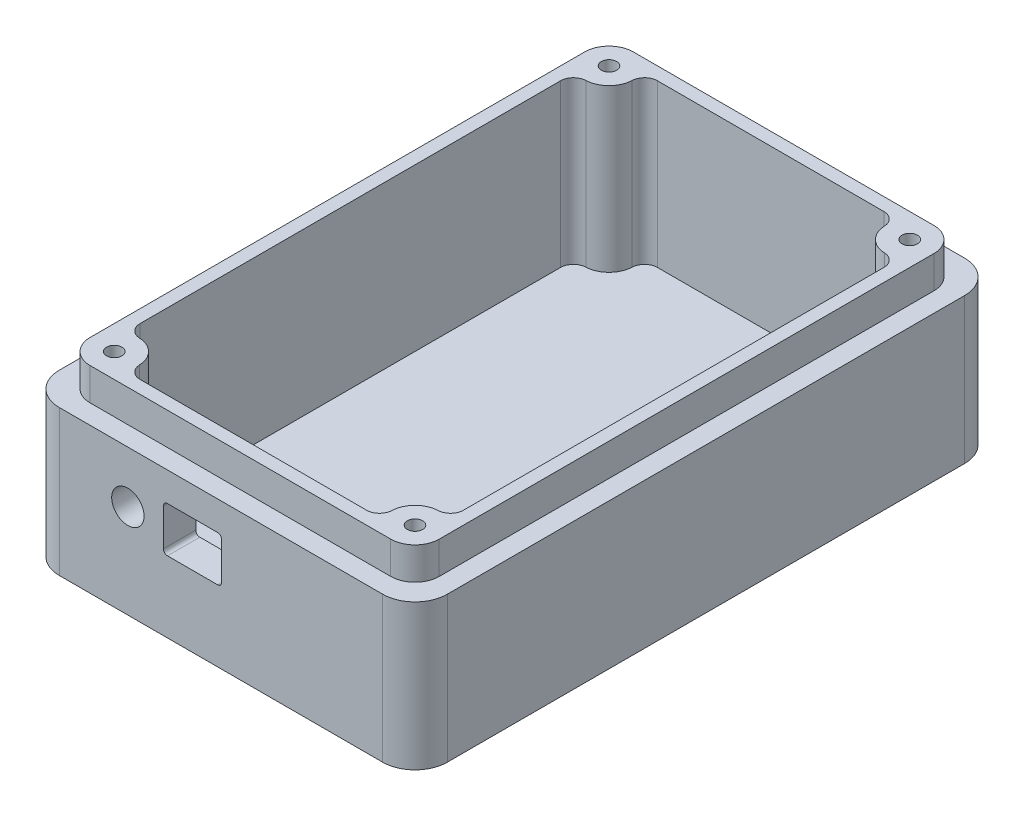
SolidWorks part; units mm, degrees
ref_plane "Front Plane" through (0, 0, 0) normal (0, 0, 1) x (1, 0, 0)
ref_plane "Top Plane" through (0, 0, 0) normal (0, 1, 0) x (1, 0, 0)
ref_plane "Right Plane" through (0, 0, 0) normal (1, 0, 0) x (0, 0, -1)
sketch "Sketch1" plane through (0, 0, 0) normal (0, 1, 0) x (1, 0, 0)
  line L1 (-38.1, -57.15) -> (38.1, -57.15)
  line L2 (-38.1, -57.15) -> (-38.1, 57.15)
  line L3 (-38.1, 57.15) -> (38.1, 57.15)
  line L4 (38.1, -57.15) -> (38.1, 57.15)
  line L5 (-38.1, -57.15) -> (38.1, 57.15) construction
  line L6 (-38.1, 57.15) -> (38.1, -57.15) construction
  point P0 (0, 0)
  dimension "D1" = 76.2
  dimension "D2" = 114.3
extrude "Boss-Extrude1" add sketch "Sketch1" along normal blind 3.175
sketch "Sketch3" plane through (0, 3.175, 0) normal (0, 1, 0) x (1, 0, 0)
  line L0 (-31.75, 50.8) -> (31.75, 50.8)
  line L1 (-38.1, 57.15) -> (38.1, 57.15)
  line L2 (-38.1, 57.15) -> (-38.1, -57.15)
  line L3 (-38.1, -57.15) -> (38.1, -57.15)
  line L4 (38.1, 57.15) -> (38.1, -57.15)
  line L5 (31.75, 50.8) -> (31.75, -50.8)
  line L6 (-31.75, -50.8) -> (31.75, -50.8)
  line L7 (-31.75, 50.8) -> (-31.75, -50.8)
  dimension "D1" = 6.35
extrude "Boss-Extrude2" add sketch "Sketch3" along normal blind 25.4
sketch "Sketch4" plane through (0, 0, 57.15) normal (0, 0, 1) x (1, 0, 0)
  line L0 (-38.1, 28.575) -> (-38.1, 0) construction
  line L5 (-11.303, 22.86) -> (0.127, 22.86)
  line L6 (-11.303, 22.86) -> (-11.303, 13.97)
  line L7 (-11.303, 13.97) -> (0.127, 13.97)
  line L8 (0.127, 22.86) -> (0.127, 13.97)
  line L9 (-11.303, 22.86) -> (0.127, 13.97) construction
  line L10 (-11.303, 13.97) -> (0.127, 22.86) construction
  line L11 (-38.1, 0) -> (38.1, 0) construction
  circle A0 centre (-18.288, 18.415) radius 3.175
  point P2 (-5.588, 18.415)
  dimension "D5" = 6.35
  dimension "D1" = 11.43
  dimension "D2" = 8.89
  dimension "D3" = 32.512
  dimension "D4" = 18.415
  dimension "D6" = 12.7
extrude "Cut-Extrude1" cut sketch "Sketch4" against normal up to next
sketch "Sketch5" plane through (0, 28.575, 0) normal (0, 1, 0) x (1, 0, 0)
  line L0 (-34.29, 53.34) -> (34.29, 53.34)
  line L1 (-31.75, 50.8) -> (31.75, 50.8)
  line L2 (-31.75, 50.8) -> (-31.75, -50.8)
  line L3 (-31.75, -50.8) -> (31.75, -50.8)
  line L4 (31.75, 50.8) -> (31.75, -50.8)
  line L5 (34.29, 53.34) -> (34.29, -53.34)
  line L6 (-34.29, -53.34) -> (34.29, -53.34)
  line L7 (-34.29, 53.34) -> (-34.29, -53.34)
  dimension "D1" = 2.54
extrude "Boss-Extrude3" add sketch "Sketch5" along normal blind 6.35
fillet "Fillet3" radius 6.35 4 edges at (38.1, 14.2875, -57.15) (38.1, 14.2875, 57.15) (-38.1, 14.2875, 57.15) (-38.1, 14.2875, -57.15)
fillet "Fillet4" radius 4.7625 4 edges at (-34.29, 31.75, -53.34) (34.29, 31.75, -53.34) (34.29, 31.75, 53.34) (-34.29, 31.75, 53.34)
fillet "Fillet5" radius 3.175 4 edges at (31.75, 19.05, 50.8) (-31.75, 19.05, 50.8) (31.75, 19.05, -50.8) (-31.75, 19.05, -50.8)
fillet "Fillet6" radius 0.7937 4 edges at (0.127, 22.86, 53.975) (0.127, 13.97, 53.975) (-11.303, 13.97, 53.975) (-11.303, 22.86, 53.975)
sketch "Sketch6" plane through (0, 3.175, 0) normal (0, 1, 0) x (1, 0, 0)
  line L0 (0, 0) -> (0, 18.0219) construction
  line L1 (0, 0) -> (16.3238, 0) construction
  circle A1 centre (-29.5275, 48.5775) radius 4.7625
  arc A2 (-29.5275, 53.34) -> (-34.29, 48.5775) centre (-29.5275, 48.5775) ccw construction
  circle A3 centre (29.5275, 48.5775) radius 4.7625
  circle A4 centre (29.5275, -48.5775) radius 4.7625
  circle A5 centre (-29.5275, -48.5775) radius 4.7625
  dimension "D1" = 9.525
extrude "Boss-Extrude4" add sketch "Sketch6" along normal up to surface (31.75 mm away) up to face at (0, 34.925, 0)
sketch "Sketch8" plane through (0, 34.925, 0) normal (0, 1, 0) x (1, 0, 0)
  line L0 (0, 0) -> (0, 14.7799) construction
  line L1 (0, 0) -> (16.191, 0) construction
  circle A0 centre (-29.5275, 48.5775) radius 1.4986
  arc A1 (-29.5275, 53.34) -> (-34.29, 48.5775) centre (-29.5275, 48.5775) ccw construction
  circle A2 centre (29.5275, 48.5775) radius 1.4986
  circle A3 centre (29.5275, -48.5775) radius 1.4986
  circle A4 centre (-29.5275, -48.5775) radius 1.4986
  dimension "D1" = 2.9972
extrude "Cut-Extrude2" cut sketch "Sketch8" against normal blind 12.7
fillet "Fillet8" radius 2.54 8 edges at (25.3154, 19.05, 50.8) (31.75, 19.05, 44.3654) (31.75, 19.05, -44.3654) (25.3154, 19.05, -50.8) (-25.3154, 19.05, -50.8) (-31.75, 19.05, -44.3654) (-25.3154, 19.05, 50.8) (-31.75, 19.05, 44.3654)
